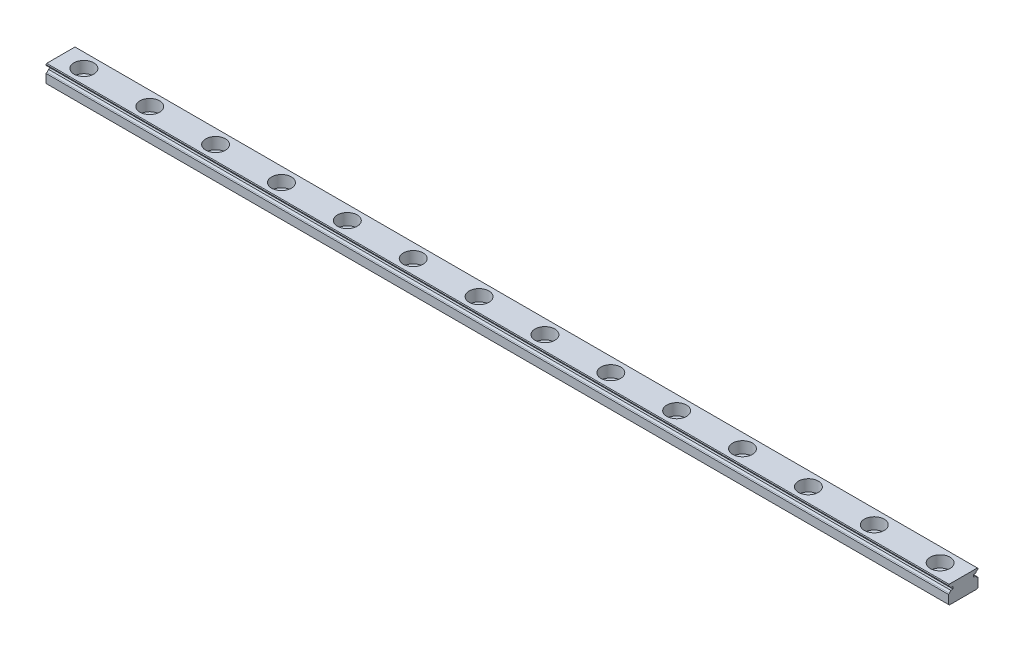
SolidWorks part; units mm, degrees
material "AISI Type 316L stainless steel"
ref_plane "Front Plane" through (0, 0, 0) normal (0, 0, 1) x (1, 0, 0)
ref_plane "Top Plane" through (0, 0, 0) normal (0, 1, 0) x (1, 0, 0)
ref_plane "Right Plane" through (0, 0, 0) normal (1, 0, 0) x (0, 0, -1)
ref_plane "Plane1" through (-7, 0, 0) normal (1, 0, 0) x (0, 0, -1)
sketch "Sketch1" plane through (-7, 0, 0) normal (1, 0, 0) x (0, 0, -1)
  line L0 (0, 5.5) -> (0, 0) construction
  line L1 (-4.5, 5.5) -> (4.5, 5.5)
  line L3 (-4.5, 0) -> (4.5, 0)
  line L10 (4.5, 5.5) -> (4.5, 0)
  line L11 (-4.5, 5.5) -> (-4.5, 0)
  dimension "H1" = 5.5
  dimension "W1" = 9
extrude "Boss-Extrude1" add sketch "Sketch1" along normal blind 274
sketch "Sketch2" plane through (-7, 0, 0) normal (1, 0, 0) x (0, 0, -1)
  line L0 (3.1, 4) -> (4.5, 4) construction
  line L1 (0, 0) -> (0, 4.35) construction
  line L2 (4.5, 5.0443) -> (4.22, 4.8826)
  line L3 (3.1, 4.35) -> (3.7533, 4.35)
  line L4 (3.1, 4.35) -> (3.1, 3.65)
  line L5 (3.1, 3.65) -> (3.7533, 3.65)
  line L6 (4.22, 3.1174) -> (4.5, 2.9557)
  line L7 (0, 5.5) -> (0, 0) construction
  line L8 (4.5, 5.0443) -> (4.5, 2.9557)
  line L9 (4.5, 5.5) -> (4.5, 0) construction
  line L10 (-4.5, 0) -> (4.5, 0) construction
  line L11 (-3.1, 4) -> (-4.5, 4) construction
  line L12 (-4.5, 5.0443) -> (-4.5, 2.9557)
  line L13 (-4.22, 3.1174) -> (-4.5, 2.9557)
  line L14 (-3.1, 3.65) -> (-3.7533, 3.65)
  line L15 (-3.1, 4.35) -> (-3.1, 3.65)
  line L16 (-3.1, 4.35) -> (-3.7533, 4.35)
  line L17 (-4.5, 5.0443) -> (-4.22, 4.8826)
  arc A0 (4.22, 4.8826) -> (3.7533, 4.35) centre (4.77, 3.93) ccw
  arc A1 (3.7533, 3.65) -> (4.22, 3.1174) centre (4.77, 4.07) ccw
  arc A2 (-3.7533, 3.65) -> (-4.22, 3.1174) centre (-4.77, 4.07) cw
  arc A3 (-4.22, 4.8826) -> (-3.7533, 4.35) centre (-4.77, 3.93) cw
  dimension "MSM_8" = 1.1
  dimension "MSM_6" = 4
  dimension "MSM_7" = 60
  dimension "MSM_2" = 0.27
  dimension "MSM_5" = 0.7
  dimension "MSM_1" = 1.4
  dimension "MSM_3" = 4.07
  dimension "MSM_4" = 3.93
extrude "Cut-Extrude1" [suppressed] cut sketch "Sketch2" along normal through all
sketch "Sketch3" plane through (-7, 0, 0) normal (1, 0, 0) x (0, 0, -1)
  line L0 (3.1, 4) -> (4.5, 4) construction
  line L1 (0, 0) -> (0, 4.35) construction
  line L2 (4.5, 5.0443) -> (4.22, 4.8826)
  line L3 (3.1, 4.35) -> (3.7533, 4.35)
  line L4 (3.1, 4.35) -> (3.1, 3.65)
  line L5 (3.1, 3.65) -> (3.7533, 3.65)
  line L6 (4.5, 2.9557) -> (4.22, 3.1174)
  line L7 (4.5, 5.5) -> (4.5, 0) construction
  line L8 (4.5, 5.0443) -> (4.5, 2.9557)
  line L9 (-4.5, 0) -> (4.5, 0) construction
  line L10 (-3.1, 4) -> (-4.5, 4) construction
  line L11 (-4.5, 5.0443) -> (-4.5, 2.9557)
  line L12 (-4.5, 2.9557) -> (-4.22, 3.1174)
  line L13 (-3.1, 3.65) -> (-3.7533, 3.65)
  line L14 (-3.1, 4.35) -> (-3.1, 3.65)
  line L15 (-3.1, 4.35) -> (-3.7533, 4.35)
  line L16 (-4.5, 5.0443) -> (-4.22, 4.8826)
  arc A0 (4.22, 4.8826) -> (3.7533, 4.35) centre (4.77, 3.93) ccw
  arc A1 (3.7533, 3.65) -> (4.22, 3.1174) centre (4.77, 4.07) ccw
  arc A2 (-3.7533, 3.65) -> (-4.22, 3.1174) centre (-4.77, 4.07) cw
  arc A3 (-4.22, 4.8826) -> (-3.7533, 4.35) centre (-4.77, 3.93) cw
  dimension "MSM_8" = 1.1
  dimension "MSM_6" = 4
  dimension "MSM_7" = 60
  dimension "MSM_2" = 0.27
  dimension "MSM_5" = 0.7
  dimension "MSM_1" = 1.4
  dimension "MSM_3" = 4.07
  dimension "MSM_4" = 3.93
extrude "Cut-Extrude2" cut sketch "Sketch3" along normal through all
hole_wizard "CBORE for Socket Head Cap Screw1" positions "Sketch5" profile "Sketch4" counterbore size "M3" standard "JIS" end condition through all
sketch "Sketch5" plane through (0, 5.5, 0) normal (0, 1, 0) x (1, 0, 0)
  line L0 (-7, -3.025) -> (-7, 3.025) construction
  point P0 (0, 0)
  dimension "G" = 7
sketch "Sketch4" plane through (0, 5.5, 0) normal (1, 0, 0) x (0, 0, 1)
  line L0 (0, 0) -> (0, 5.5)
  line L1 (0, 5.5) -> (1.75, 5.5)
  line L3 (1.75, 5.5) -> (1.75, 3.5)
  line L4 (1.75, 3.5) -> (3, 3.5)
  line L5 (3, 3.5) -> (3, 0)
  line L7 (3, 0) -> (0, 0)
  line L11 (0, 0) -> (0, 5.5) construction
  dimension "D1_s" = 3.5
  dimension "Thru Hole Depth" = 5.5
  dimension "D2_s" = 6
  dimension "H_s" = 3.5
pattern_linear "LPattern1" count 14 spacing 20 along (1, 0, 0) of "CBORE for Socket Head Cap Screw1"
chamfer "Chamfer1" distance 0.2 2 edges at (130, 5.5, 4.5) (130, 5.5, -4.5)
chamfer "Chamfer2" distance 0.3 2 edges at (130, 0, -4.5) (130, 0, 4.5)
ref_plane "Plane2" [suppressed] through (0, 5.5, 0) normal (0, 1, 0) x (1, 0, 0)
hole_wizard "Tap1" [suppressed] positions "Sketch7" profile "Sketch6" hole size "M3x0.5" standard "JIS"
sketch "Sketch7" [suppressed] plane through (0, 5.5, 0) normal (0, 1, 0) x (1, 0, 0)
  line L0 (-7.5, -3.025) -> (-7.5, 3.025) construction
  point P0 (0, 0)
  dimension "G" = 7
sketch "Sketch6" [suppressed] plane through (0, 5.5, 0) normal (1, 0, 0) x (0, 0, 1)
  line L0 (0, 0) -> (0, 5.5)
  line L1 (0, 5.5) -> (1.621, 5.5)
  line L2 (1.621, 5.5) -> (1.621, 0)
  line L5 (1.621, 0) -> (0, 0)
  line L11 (0, 0) -> (0, 5.5) construction
  dimension "STD_1" = 3.242
  dimension "Thru Hole Depth" = 5.5
cosmetic thread "Thread1" [suppressed] parameters "MC"=4
pattern_linear "LPattern2" [suppressed]
sketch "Sketch8" [suppressed] plane through (0, 0, 0) normal (0, 0, 1) x (1, 0, 0)
  line L0 (-7.5, -3.025) -> (-7.5, 3.025) construction
  line L1 (-7.5, 5.5) -> (-5, 5.5)
  line L2 (-7.5, 5.5) -> (-7.5, 0)
  line L3 (-7.5, 0) -> (-5, 0)
  line L4 (-5, 5.5) -> (-5, 0)
  line L5 (0, 5.5) -> (0, 0) construction
  dimension "LLC" = 2.5
  dimension "N" = 5
extrude "Cut-Extrude3" [suppressed] cut sketch "Sketch8" against normal through all and the other way through all
sketch "Sketch9" [suppressed] plane through (0, 0, 0) normal (0, 0, 1) x (1, 0, 0)
  line L0 (-7.5, 5.5) -> (-7.5, 0) construction
  line L1 (25, 5.5) -> (27.5, 5.5)
  line L2 (25, 5.5) -> (25, 0)
  line L3 (25, 0) -> (27.5, 0)
  line L4 (27.5, 5.5) -> (27.5, 0)
  line L5 (-7.5, -3.025) -> (-7.5, 3.025) construction
  line L8 (22.5, 5.5) -> (22.5, 0) construction
  dimension "L" = 274
  dimension "RLC" = 2.5
  dimension "N" = 2.5
extrude "Cut-Extrude4" [suppressed] cut sketch "Sketch9" against normal through all and the other way through all
